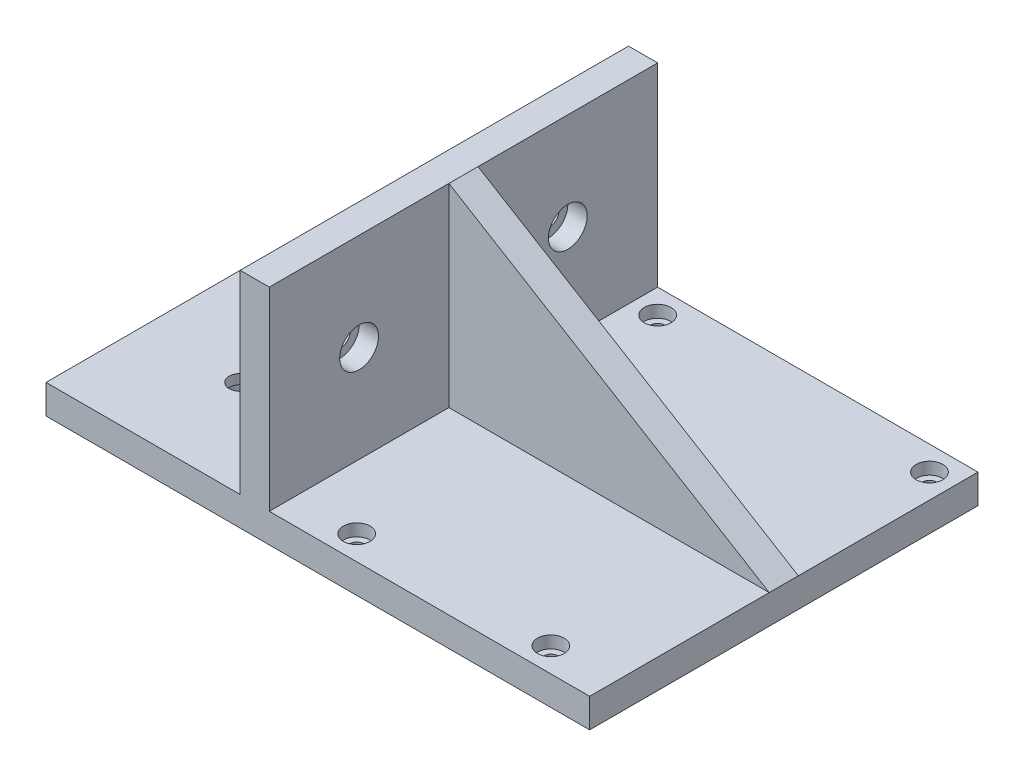
SolidWorks part; units mm, degrees
ref_plane "Front Plane" through (0, 0, 0) normal (0, 0, 1) x (1, 0, 0)
ref_plane "Top Plane" through (0, 0, 0) normal (0, 1, 0) x (1, 0, 0)
ref_plane "Right Plane" through (0, 0, 0) normal (1, 0, 0) x (0, 0, -1)
sketch "Sketch1" plane through (0, 0, 0) normal (0, 1, 0) x (1, 0, 0)
  line L0 (-28, 35) -> (28, 35) construction
  line L1 (28, 35) -> (20, -35) construction
  line L2 (20, -35) -> (-20, -35) construction
  line L3 (-20, -35) -> (-28, 35) construction
  line L5 (0, 35) -> (0, -35) construction
  line L7 (-33, -40) -> (33, -40)
  line L8 (-33, -40) -> (-33, 40)
  line L9 (-33, 40) -> (33, 40)
  line L10 (33, -40) -> (33, 40)
  line L11 (-33, -40) -> (33, 40) construction
  line L12 (-33, 40) -> (33, -40) construction
  point P6 (0, 0)
  point P7 (0, 0)
  point P13 (0, 0)
  dimension "D1" = 56
  dimension "D2" = 40
  dimension "D3" = 70
  dimension "D4" = 5
  dimension "D5" = 5
extrude "Boss-Extrude1" add sketch "Sketch1" along normal blind 6
sketch "Sketch2" plane through (0, 6, 0) normal (0, 1, 0) x (1, 0, 0)
  line L0 (-28, 35) -> (28, 35) construction
  line L1 (28, 35) -> (20, -35) construction
  line L2 (20, -35) -> (-20, -35) construction
  line L3 (-20, -35) -> (-28, 35) construction
  line L5 (0, 35) -> (0, -35) construction
  point P0 (-28, 35)
  point P1 (28, 35)
  point P3 (20, -35)
  point P4 (-20, -35)
  point P6 (0, 0)
  point P19 (-28, 35)
  point P21 (28, 35)
  point P23 (-20, -35)
  point P25 (20, -35)
  dimension "D1" = 40
  dimension "D2" = 56
  dimension "D3" = 70
hole_wizard "CBORE for M2.5 SHCS2" positions "Sketch2" profile "Sketch3" counterbore size "M2.5" standard "ANSI Metric" end condition up to next
sketch "Sketch3" plane through (20, 6, 35) normal (1, 0, 0) x (0, 0, 1)
  line L0 (0, 0) -> (0, 6)
  line L1 (0, 6) -> (1.45, 6)
  line L3 (1.45, 6) -> (1.45, 2.5)
  line L4 (1.45, 2.5) -> (2.75, 2.5)
  line L5 (2.75, 2.5) -> (2.75, 0)
  line L7 (2.75, 0) -> (0, 0)
  line L11 (0, -6.35) -> (0, 107.95) construction
  dimension "Thru Hole Dia." = 2.9
  dimension "Thru Hole Depth" = 6
  dimension "C'Bore Dia." = 5.5
  dimension "C'Bore Depth" = 2.5
sketch "Sketch4" plane through (0, 0, 40) normal (0, 0, 1) x (1, 0, 0)
  line L11 (-33, 6) -> (-39, 6)
  line L12 (-33, 0) -> (-79, 0)
  line L13 (-33, 0) -> (-33, 6)
  line L14 (-33, 6) -> (-79, 6)
  line L15 (-79, 0) -> (-79, 6)
  line L16 (-33, 6) -> (-33, 46)
  line L17 (-33, 46) -> (-39, 46)
  line L18 (-39, 6) -> (-39, 46)
  dimension "D1" = 40
  dimension "D2" = 6
  dimension "D3" = 40
extrude "Boss-Extrude2" add sketch "Sketch4" against normal up to surface (80 mm away) up to face at (0, 3, -40)
sketch "Sketch5" plane through (0, 0, 0) normal (0, 0, 1) x (1, 0, 0)
  line L0 (-33, 46) -> (33, 6)
rib "Rib1" sketch "Sketch5" sketch "Sketch5" thickness 6 extrusion direction parallel to sketch draft on no parameters "D1"=6
hole_wizard "CBORE for M4 SHCS1" positions "3DSketch1" profile "Sketch6" counterbore size "M4" standard "ANSI Metric" end condition up to next
sketch3d "3DSketch1"
  line L0 (-33, 26, -40) -> (-33, 26, -3) construction
  line L1 (-33, 46, -40) -> (-33, 6, -40) construction
  line L2 (-33, 46, -3) -> (-33, 6, -3) construction
  line L4 (-33, 26, 40) -> (-33, 26, 3) construction
  line L5 (-33, 6, 40) -> (-33, 46, 40) construction
  line L6 (-33, 46, 3) -> (-33, 6, 3) construction
  line L7 (-39, 6, 40) -> (-39, 6, -40) construction
  line L9 (-39, 6, 0) -> (-79, 6, 0) construction
  line L10 (-79, 6, -40) -> (-79, 6, 40) construction
  line L11 (-59, 6, 0) -> (-59, 6, -40) construction
  line L12 (-79, 6, -40) -> (-39, 6, -40) construction
  line L14 (-59, 6, 0) -> (-59, 6, 40) construction
  line L15 (-39, 6, 40) -> (-79, 6, 40) construction
  point P19 (-33, 26, -21.5)
  point P21 (-33, 26, 21.5)
  point P26 (-33, 26, 21.5)
  point P30 (-33, 26, -21.5)
  point P41 (-59, 0, 20)
  point P43 (-59, 0, -20)
  point P56 (0, 0, 0)
  point P57 (-59, 6, 20)
  point P58 (0, 0, 0)
  point P59 (-59, 6, -20)
sketch "Sketch6" plane through (-59, 0, -20) normal (1, 0, 0) x (0, 0, -1)
  line L0 (0, 0) -> (0, 6)
  line L1 (0, 6) -> (2.25, 6)
  line L3 (2.25, 6) -> (2.25, 4)
  line L4 (2.25, 4) -> (4, 4)
  line L5 (4, 4) -> (4, 0)
  line L7 (4, 0) -> (0, 0)
  line L11 (0, -6.35) -> (0, 107.95) construction
  dimension "Thru Hole Dia." = 4.5
  dimension "Thru Hole Depth" = 6
  dimension "C'Bore Dia." = 8
  dimension "C'Bore Depth" = 4
